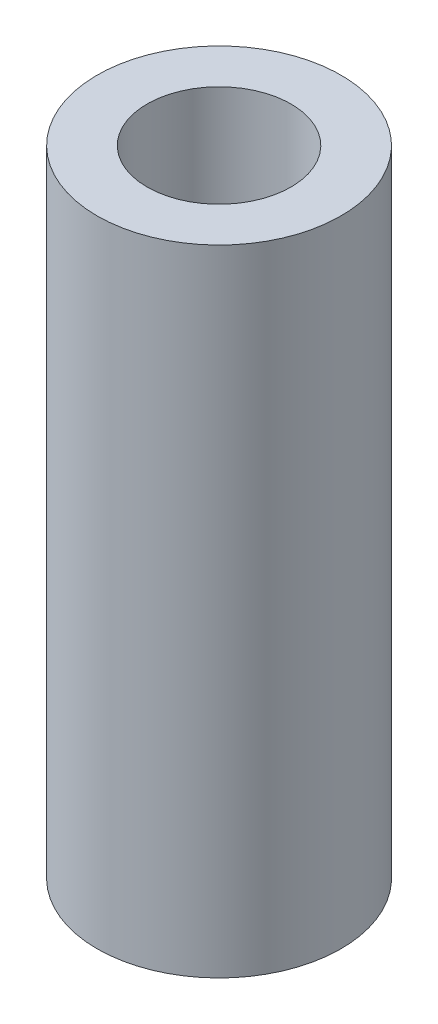
SolidWorks part; units mm, degrees
ref_plane "Front Plane" through (0, 0, 0) normal (0, 0, 1) x (1, 0, 0)
ref_plane "Top Plane" through (0, 0, 0) normal (0, 1, 0) x (1, 0, 0)
ref_plane "Right Plane" through (0, 0, 0) normal (1, 0, 0) x (0, 0, -1)
sketch "Sketch1" plane through (0, 0, 0) normal (0, 1, 0) x (1, 0, 0)
  circle A0 centre (0, 0) radius 3.6
  circle A1 centre (0, 0) radius 6.1
  dimension "D1" = 7.2
  dimension "D2" = 12.2
extrude "Boss-Extrude1" add sketch "Sketch1" along normal blind 31.75
